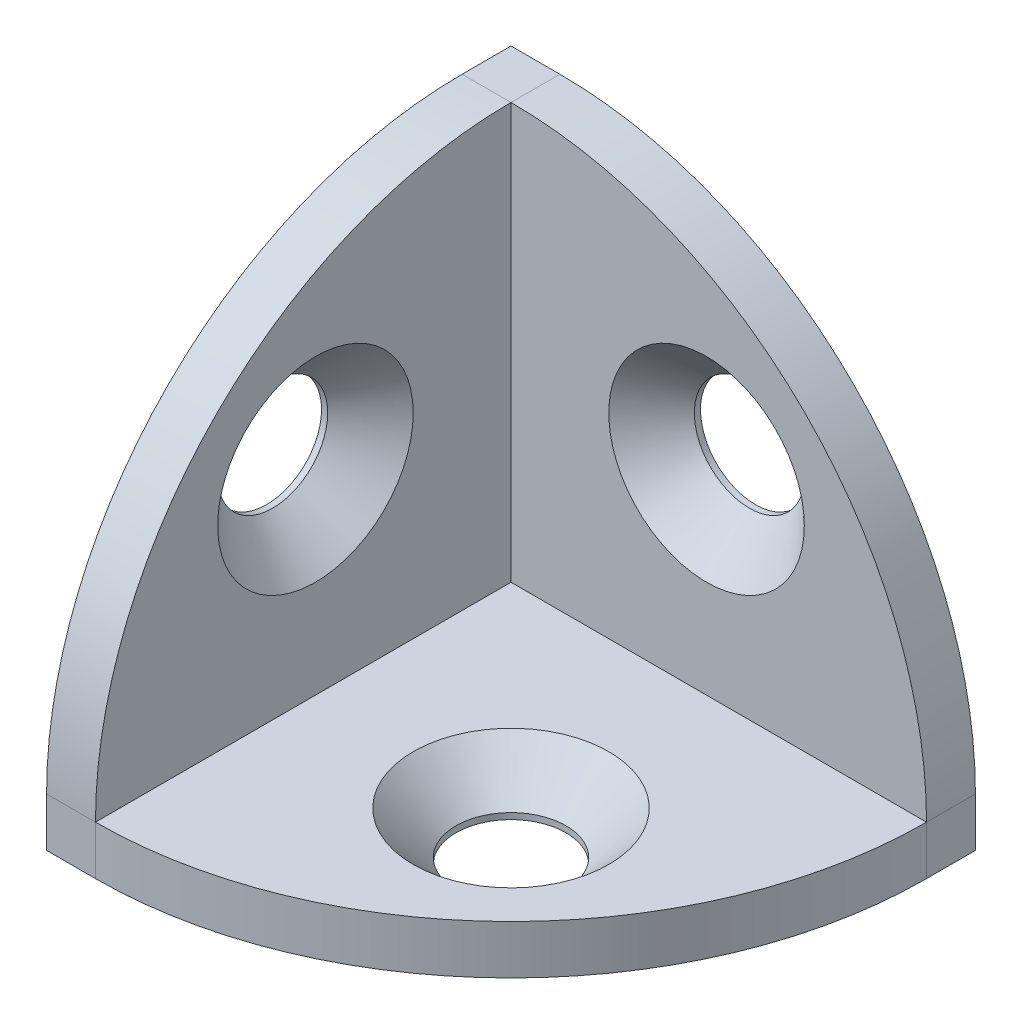
SolidWorks part; units mm, degrees
material "Алюминиевый сплав"
ref_plane "Спереди" through (0, 0, 0) normal (0, 0, 1) x (1, 0, 0)
ref_plane "Сверху" through (0, 0, 0) normal (0, 1, 0) x (1, 0, 0)
ref_plane "Справа" through (0, 0, 0) normal (1, 0, 0) x (0, 0, -1)
sketch "Эскиз1" plane through (0, 0, 0) normal (0, 0, 1) x (1, 0, 0)
  line L0 (0, 0) -> (0, 38)
  line L1 (0, 38) -> (4, 38)
  line L2 (38, 4) -> (38, 0)
  line L3 (38, 0) -> (0, 0)
  arc A0 (4, 38) -> (38, 4) centre (4, 4) cw
  dimension "D1" = 38
  dimension "D2" = 4
extrude "Бобышка-Вытянуть1" add sketch "Эскиз1" along normal blind 4
hole_wizard "Зенковка для винта с полупотайной головкой M81" positions "Эскиз2" profile "Эскиз3" countersink size "M8" standard "ISO"
sketch "Эскиз2" plane through (0, 0, 4) normal (0, 0, 1) x (1, 0, 0)
  line L0 (0, 0) -> (38, 0) construction
  line L1 (20, 20) -> (0, 20)
  line L2 (0, 38) -> (0, 0) construction
  line L4 (20, 20) -> (20, 0)
  point P0 (20, 20)
  dimension "D1" = 20
sketch "Эскиз3" plane through (20, 20, 4) normal (1, 0, 0) x (0, -1, 0)
  line L0 (0, 0) -> (0, 11.9539)
  line L1 (0, 11.9539) -> (4.5, 9.25)
  line L2 (4.5, 9.25) -> (4.5, 3.5)
  line L3 (4.5, 3.5) -> (8, 0)
  line L5 (8, 0) -> (0, 0)
  line L6 (-4.5, 3.5) -> (-8, 0) construction
  line L10 (0, 11.9539) -> (-4.5, 9.25) construction
  line L11 (0, -6.35) -> (0, 107.95) construction
  dimension "Диаметр отверстия" = 9
  dimension "Глубина отверстия" = 9.25
  dimension "Диаметр передней зенковки" = 16
  dimension "Угол передней зенковки" = 90
  dimension "Угол заточки сверла" = 118
sketch "Эскиз4" plane through (0, 0, 0) normal (0, 0, -1) x (-1, 0, 0)
  line L0 (-20, 20) -> (-20, 3) construction
  line L1 (-3, 24) -> (-1.5, 24)
  line L2 (-3, 24) -> (-3, 16)
  line L3 (-3, 16) -> (-1.5, 16)
  line L4 (-1.5, 24) -> (-1.5, 16)
  line L5 (-24, 3) -> (-16, 3)
  line L6 (-24, 3) -> (-24, 1.5)
  line L7 (-24, 1.5) -> (-16, 1.5)
  line L8 (-16, 3) -> (-16, 1.5)
  line L9 (-20, 20) -> (-3, 20) construction
  line L10 (0, 38) -> (0, 0) construction
  point P12 (-10.346, 4.0183)
  point P15 (-14, 3.543)
  dimension "D1" = 1.5
  dimension "D2" = 1.5
  dimension "D3" = 8
extrude "Бобышка-Вытянуть2" add sketch "Эскиз4" along normal blind 1
ref_plane "Плоскость1" through (0, 0, 0) normal (0, -0.7071, 0.7071) x (1, 0, 0)
ref_plane "Плоскость2" through (0, 0, 0) normal (-0.7071, 0, 0.7071) x (0.7071, 0, 0.7071)
mirror "Зеркальное отражение1" about plane through (0, 0, 0) normal (0, -0.7071, 0.7071) of "Бобышка-Вытянуть2", "Бобышка-Вытянуть1", "Зенковка для винта с полупотайной головкой M81"
mirror "Зеркальное отражение2" about plane through (0, 0, 0) normal (-0.7071, 0, 0.7071) of "Зеркальное отражение1", "Бобышка-Вытянуть1", "Зенковка для винта с полупотайной головкой M81", "Бобышка-Вытянуть2"
